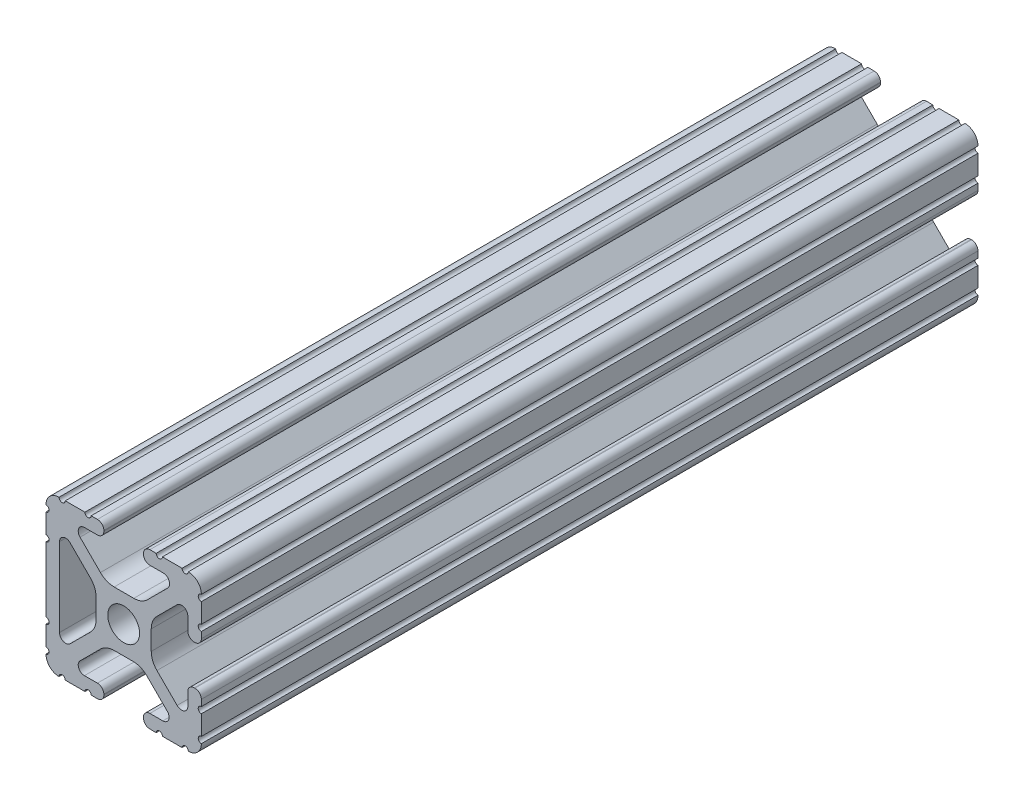
SolidWorks part; units mm, degrees
material "6061-T6 (SS)"
ref_plane "Front Plane" through (0, 0, 0) normal (0, 0, 1) x (1, 0, 0)
ref_plane "Top Plane" through (0, 0, 0) normal (0, 1, 0) x (1, 0, 0)
ref_plane "Right Plane" through (0, 0, 0) normal (1, 0, 0) x (0, 0, -1)
ref_plane "Plane1" through (0, 0, -152.4) normal (0, 0, -1) x (-1, 0, 0)
sketch "Sketch1" plane through (0, 0, -152.4) normal (0, 0, -1) x (-1, 0, 0)
  line L0 (6.4164, -10.4902) -> (4.2875, -10.4902)
  line L1 (3.2385, -11.5392) -> (3.2385, -11.651)
  line L2 (4.2875, -12.7) -> (5.3171, -12.7)
  line L3 (6.3331, -12.7) -> (9.5504, -12.7)
  line L4 (12.7, -9.5504) -> (12.7, -6.3331)
  line L5 (12.7, -5.3171) -> (12.7, 5.3171)
  line L6 (12.7, 6.3331) -> (12.7, 9.5504)
  line L7 (9.5504, 12.7) -> (6.3331, 12.7)
  line L8 (5.3171, 12.7) -> (4.2875, 12.7)
  line L9 (3.2384, 11.651) -> (3.2384, 11.5392)
  line L10 (4.2875, 10.4902) -> (6.4164, 10.4902)
  line L11 (7.1341, 8.7551) -> (3.7966, 5.4237)
  line L12 (1.5536, 4.4958) -> (-1.6573, 4.4958)
  line L13 (-3.9003, 5.4237) -> (-7.2072, 8.7245)
  line L14 (-6.4768, 10.4902) -> (-4.2875, 10.4902)
  line L15 (-3.2384, 11.5392) -> (-3.2384, 11.651)
  line L16 (-4.2875, 12.7) -> (-5.3171, 12.7)
  line L17 (-6.3331, 12.7) -> (-9.5504, 12.7)
  line L18 (-12.7, 9.5504) -> (-12.7, 6.3331)
  line L19 (-12.7, 5.3171) -> (-12.7, 4.2875)
  line L20 (-11.651, 3.2385) -> (-11.5392, 3.2385)
  line L21 (-10.4902, 4.2875) -> (-10.4902, 6.4021)
  line L22 (-8.737, 7.1292) -> (-5.4405, 3.8388)
  line L23 (-4.5085, 1.5917) -> (-4.5085, -1.5917)
  line L24 (-5.4405, -3.8388) -> (-8.737, -7.1292)
  line L25 (-10.4902, -6.4021) -> (-10.4902, -4.2875)
  line L26 (-11.5392, -3.2385) -> (-11.651, -3.2385)
  line L27 (-12.7, -4.2875) -> (-12.7, -5.3171)
  line L28 (-12.7, -6.3331) -> (-12.7, -9.5504)
  line L29 (-9.5504, -12.7) -> (-6.3331, -12.7)
  line L30 (-5.3171, -12.7) -> (-4.2875, -12.7)
  line L31 (-3.2385, -11.651) -> (-3.2385, -11.5392)
  line L32 (-4.2875, -10.4902) -> (-6.4083, -10.4902)
  line L33 (-7.1285, -8.7494) -> (-3.7967, -5.4237)
  line L34 (-1.5536, -4.4958) -> (1.5536, -4.4958)
  line L35 (3.7967, -5.4237) -> (7.1342, -8.7551)
  line L36 (10.4902, 6.4464) -> (10.4902, -6.4254)
  line L37 (8.7534, -7.1457) -> (5.4405, -3.8388)
  line L38 (4.5085, -1.5917) -> (4.5085, 1.5917)
  line L39 (5.4405, 3.8388) -> (8.7683, 7.1606)
  arc A0 (4.2875, -10.4902) -> (3.2385, -11.5392) centre (4.2875, -11.5392) ccw
  arc A1 (3.2385, -11.651) -> (4.2875, -12.7) centre (4.2875, -11.651) ccw
  arc A2 (5.3171, -12.7) -> (6.3331, -12.7) centre (5.8251, -12.7) cw
  arc A3 (9.5504, -12.7) -> (10.5664, -12.6998) centre (10.0584, -12.7) cw
  arc A4 (10.5664, -12.6998) -> (12.6998, -10.5664) centre (10.5918, -10.5918) ccw
  arc A5 (12.6998, -10.5664) -> (12.7, -9.5504) centre (12.7, -10.0584) cw
  arc A6 (12.7, -6.3331) -> (12.7, -5.3171) centre (12.7, -5.8251) cw
  arc A7 (12.7, 5.3171) -> (12.7, 6.3331) centre (12.7, 5.8251) cw
  arc A8 (12.7, 9.5504) -> (12.6998, 10.5664) centre (12.7, 10.0584) cw
  arc A9 (12.6998, 10.5664) -> (10.5664, 12.6998) centre (10.5918, 10.5918) ccw
  arc A10 (10.5664, 12.6998) -> (9.5504, 12.7) centre (10.0584, 12.7) cw
  arc A11 (6.3331, 12.7) -> (5.3171, 12.7) centre (5.8251, 12.7) cw
  arc A12 (4.2875, 12.7) -> (3.2384, 11.651) centre (4.2875, 11.651) ccw
  arc A13 (3.2384, 11.5392) -> (4.2875, 10.4902) centre (4.2875, 11.5392) ccw
  arc A14 (6.4164, 10.4902) -> (7.1341, 8.7551) centre (6.4164, 9.4742) cw
  arc A15 (3.7966, 5.4237) -> (1.5536, 4.4958) centre (1.5536, 7.6708) cw
  arc A16 (-1.6573, 4.4958) -> (-3.9003, 5.4237) centre (-1.6573, 7.6708) cw
  arc A17 (-7.2072, 8.7245) -> (-6.4768, 10.4902) centre (-6.4768, 9.4563) cw
  arc A18 (-4.2875, 10.4902) -> (-3.2384, 11.5392) centre (-4.2875, 11.5392) ccw
  arc A19 (-3.2384, 11.651) -> (-4.2875, 12.7) centre (-4.2875, 11.651) ccw
  arc A20 (-5.3171, 12.7) -> (-6.3331, 12.7) centre (-5.8251, 12.7) cw
  arc A21 (-9.5504, 12.7) -> (-10.5664, 12.6998) centre (-10.0584, 12.7) cw
  arc A22 (-10.5664, 12.6998) -> (-12.6998, 10.5664) centre (-10.5918, 10.5918) ccw
  arc A23 (-12.6998, 10.5664) -> (-12.7, 9.5504) centre (-12.7, 10.0584) cw
  arc A24 (-12.7, 6.3331) -> (-12.7, 5.3171) centre (-12.7, 5.8251) cw
  arc A25 (-12.7, 4.2875) -> (-11.651, 3.2385) centre (-11.651, 4.2875) ccw
  arc A26 (-11.5392, 3.2385) -> (-10.4902, 4.2875) centre (-11.5392, 4.2875) ccw
  arc A27 (-10.4902, 6.4021) -> (-8.737, 7.1292) centre (-9.4628, 6.4021) cw
  arc A28 (-5.4405, 3.8388) -> (-4.5085, 1.5917) centre (-7.6835, 1.5917) cw
  arc A29 (-4.5085, -1.5917) -> (-5.4405, -3.8388) centre (-7.6835, -1.5917) cw
  arc A30 (-8.737, -7.1292) -> (-10.4902, -6.4021) centre (-9.4628, -6.4021) cw
  arc A31 (-10.4902, -4.2875) -> (-11.5392, -3.2385) centre (-11.5392, -4.2875) ccw
  arc A32 (-11.651, -3.2385) -> (-12.7, -4.2875) centre (-11.651, -4.2875) ccw
  arc A33 (-12.7, -5.3171) -> (-12.7, -6.3331) centre (-12.7, -5.8251) cw
  arc A34 (-12.7, -9.5504) -> (-12.6998, -10.5664) centre (-12.7, -10.0584) cw
  arc A35 (-12.6998, -10.5664) -> (-10.5664, -12.6998) centre (-10.5918, -10.5918) ccw
  arc A36 (-10.5664, -12.6998) -> (-9.5504, -12.7) centre (-10.0584, -12.7) cw
  arc A37 (-6.3331, -12.7) -> (-5.3171, -12.7) centre (-5.8251, -12.7) cw
  arc A38 (-4.2875, -12.7) -> (-3.2385, -11.651) centre (-4.2875, -11.651) ccw
  arc A39 (-3.2385, -11.5392) -> (-4.2875, -10.4902) centre (-4.2875, -11.5392) ccw
  arc A40 (-6.4083, -10.4902) -> (-7.1285, -8.7494) centre (-6.4083, -9.4709) cw
  arc A41 (-3.7967, -5.4237) -> (-1.5536, -4.4958) centre (-1.5536, -7.6708) cw
  arc A42 (1.5536, -4.4958) -> (3.7967, -5.4237) centre (1.5536, -7.6708) cw
  arc A43 (7.1342, -8.7551) -> (6.4164, -10.4902) centre (6.4164, -9.4742) cw
  arc A44 (8.7683, 7.1606) -> (10.4902, 6.4464) centre (9.4812, 6.4464) cw
  arc A45 (10.4902, -6.4254) -> (8.7534, -7.1457) centre (9.4724, -6.4254) cw
  arc A46 (5.4405, -3.8388) -> (4.5085, -1.5917) centre (7.6835, -1.5917) cw
  arc A47 (4.5085, 1.5917) -> (5.4405, 3.8388) centre (7.6835, 1.5917) cw
  circle A48 centre (0, 0) radius 2.6035
extrude "Boss-Extrude1" add sketch "Sketch1" against normal blind 127
